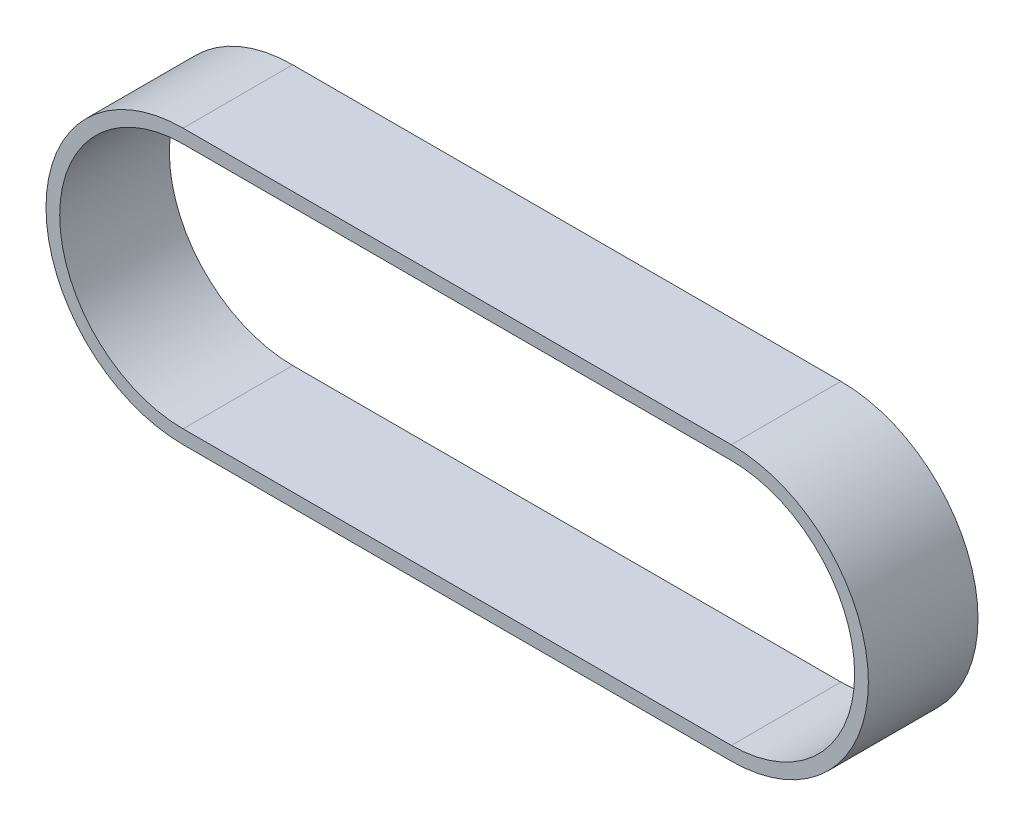
SolidWorks part; units mm, degrees
ref_plane "Front Plane" through (0, 0, 0) normal (0, 0, 1) x (1, 0, 0)
ref_plane "Top Plane" through (0, 0, 0) normal (0, 1, 0) x (1, 0, 0)
ref_plane "Right Plane" through (0, 0, 0) normal (1, 0, 0) x (0, 0, -1)
sketch "Sketch1" plane through (0, 0, 0) normal (0, 0, 1) x (1, 0, 0)
  line L0 (-50, 0) -> (50, 0) construction
  line L1 (-50, 25) -> (50, 25)
  line L2 (50, -25) -> (-50, -25)
  line L3 (-50, 22.5) -> (50, 22.5)
  line L4 (50, -22.5) -> (-50, -22.5)
  arc A0 (50, -25) -> (50, 25) centre (50, 0) ccw
  arc A1 (-50, 25) -> (-50, -25) centre (-50, 0) ccw
  arc A2 (-50, 22.5) -> (-50, -22.5) centre (-50, 0) ccw
  arc A3 (50, -22.5) -> (50, 22.5) centre (50, 0) ccw
  point P4 (0, 0)
  dimension "D1" = 50
  dimension "D3" = 45
  dimension "D2" = 100
extrude "Boss-Extrude1" add sketch "Sketch1" along normal blind 20
